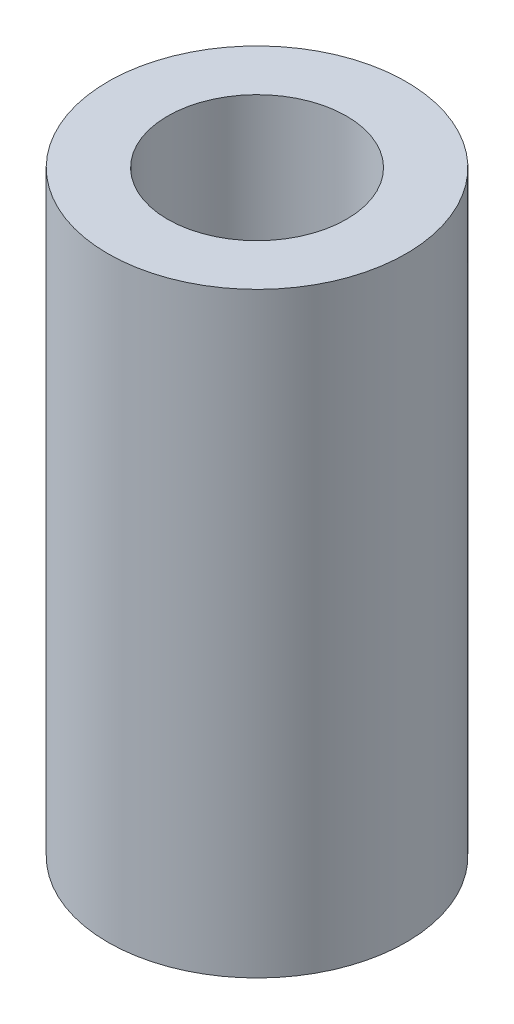
SolidWorks part; units mm, degrees
ref_plane "前视基准面" through (0, 0, 0) normal (0, 0, 1) x (1, 0, 0)
ref_plane "上视基准面" through (0, 0, 0) normal (0, 1, 0) x (1, 0, 0)
ref_plane "右视基准面" through (0, 0, 0) normal (1, 0, 0) x (0, 0, -1)
sketch "草图1" plane through (0, 0, 0) normal (0, 1, 0) x (1, 0, 0)
  line L0 (-1.245, -1.3) -> (1.245, -1.3)
  arc A0 (1.245, -1.3) -> (-1.245, -1.3) centre (0, 0) ccw
  circle A1 centre (0, 0) radius 3
  point P87 (0, 0)
  dimension "D1" = 3.6
  dimension "D3" = 6
  dimension "D2" = 1.3
extrude "凸台-拉伸1" add sketch "草图1" along normal blind 8 contours A1 A0 L0
sketch "草图2" plane through (0, 8, 0) normal (0, 1, 0) x (1, 0, 0)
  circle A0 centre (0, 0) radius 1.8
  circle A1 centre (0, 0) radius 3
  dimension "D1" = 3.6
extrude "凸台-拉伸2" add sketch "草图2" along normal blind 4
